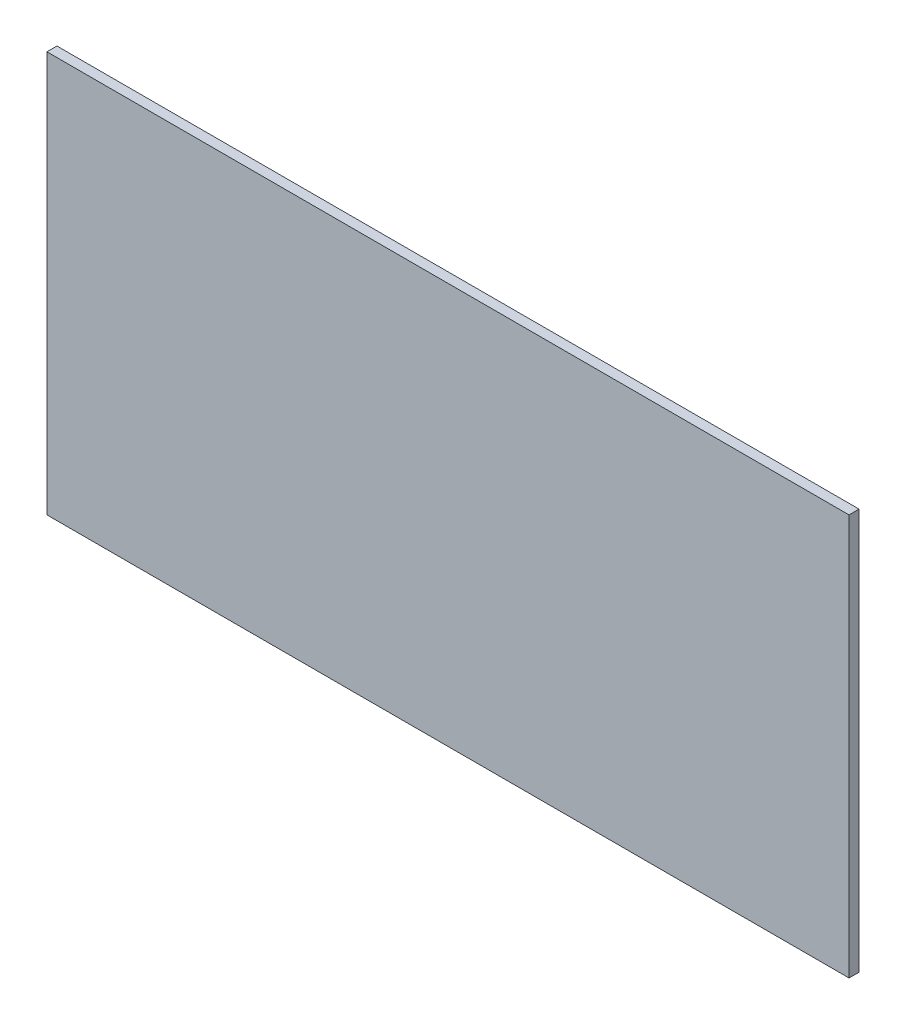
SolidWorks part; units mm, degrees
ref_plane "Front Plane" through (0, 0, 0) normal (0, 0, 1) x (1, 0, 0)
ref_plane "Top Plane" through (0, 0, 0) normal (0, 1, 0) x (1, 0, 0)
ref_plane "Right Plane" through (0, 0, 0) normal (1, 0, 0) x (0, 0, -1)
sketch "Sketch1" plane through (0, 0, 0) normal (0, 0, 1) x (1, 0, 0)
  line L1 (-127, -63.5) -> (127, -63.5)
  line L2 (-127, -63.5) -> (-127, 63.5)
  line L3 (-127, 63.5) -> (127, 63.5)
  line L4 (127, -63.5) -> (127, 63.5)
  line L5 (-127, -63.5) -> (127, 63.5) construction
  line L6 (-127, 63.5) -> (127, -63.5) construction
  point P0 (0, 0)
  dimension "D1" = 254
  dimension "D2" = 127
extrude "Boss-Extrude1" add sketch "Sketch1" along normal mid plane 3.175
